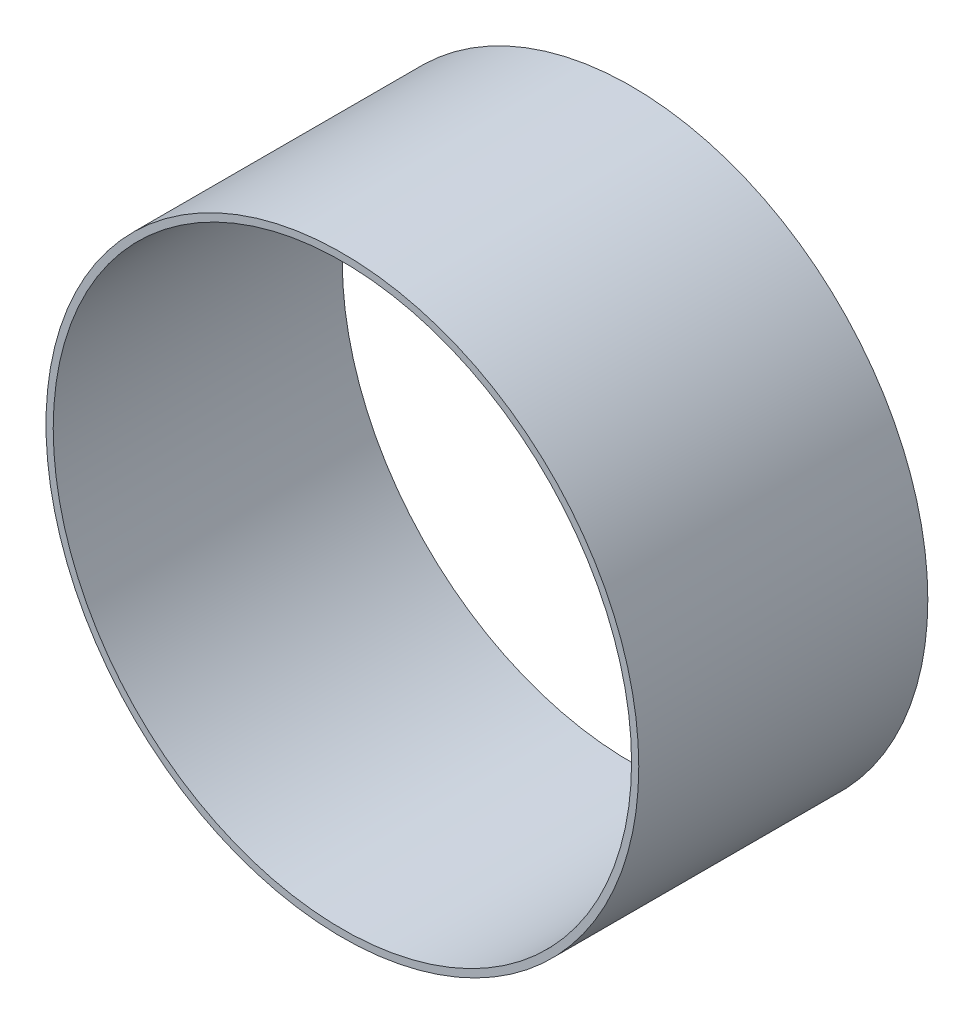
SolidWorks part; units mm, degrees
ref_plane "Front Plane" through (0, 0, 0) normal (0, 0, 1) x (1, 0, 0)
ref_plane "Top Plane" through (0, 0, 0) normal (0, 1, 0) x (1, 0, 0)
ref_plane "Right Plane" through (0, 0, 0) normal (1, 0, 0) x (0, 0, -1)
sketch "Sketch1" plane through (0, 0, 0) normal (0, 0, 1) x (1, 0, 0)
  circle A0 centre (0, 0) radius 41.016
  dimension "D1" = 82.032
extrude "Extrude-Thin1" add sketch "Sketch1" along normal mid plane 40 thin thin type one direction reverse wall 1
